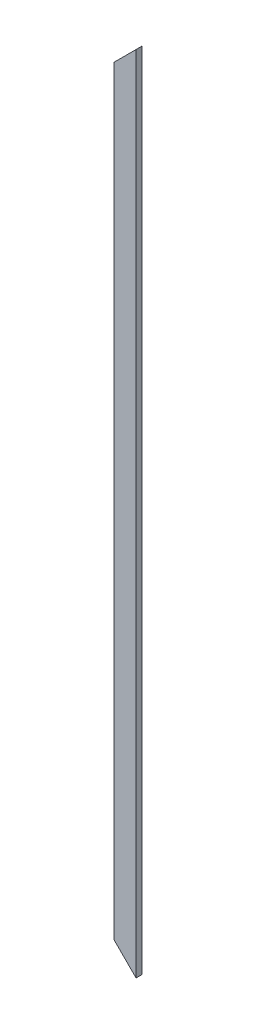
SolidWorks part; units mm, degrees
material "Oak"
ref_plane "Front Plane" through (0, 0, 0) normal (0, 0, 1) x (1, 0, 0)
ref_plane "Top Plane" through (0, 0, 0) normal (0, 1, 0) x (1, 0, 0)
ref_plane "Right Plane" through (0, 0, 0) normal (1, 0, 0) x (0, 0, -1)
sketch "Sketch1" plane through (0, 0, 0) normal (0, 1, 0) x (1, 0, 0)
  line L1 (-69.85, -19.05) -> (69.85, -19.05)
  line L2 (-69.85, -19.05) -> (-69.85, 19.05)
  line L3 (-69.85, 19.05) -> (69.85, 19.05)
  line L4 (69.85, -19.05) -> (69.85, 19.05)
  line L5 (-69.85, -19.05) -> (69.85, 19.05) construction
  line L6 (-69.85, 19.05) -> (69.85, -19.05) construction
  point P0 (0, 0)
  dimension "D1" = 38.1
  dimension "D2" = 139.7
extrude "Boss-Extrude1" add sketch "Sketch1" along normal blind 5054.6 contours L1 L4 L3 L2
sketch "Sketch2" plane through (0, 0, -19.05) normal (0, 0, -1) x (-1, 0, 0)
  line L0 (-69.85, 0) -> (69.85, 139.7)
  line L1 (69.85, 5054.6) -> (69.85, 0) construction
  line L2 (-69.85, 5054.6) -> (69.85, 4914.9)
  line L3 (69.85, 4914.9) -> (69.85, 5054.6)
  line L4 (69.85, 5054.6) -> (-69.85, 5054.6)
  line L5 (69.85, 139.7) -> (69.85, 0)
  line L6 (69.85, 0) -> (-69.85, 0)
extrude "Cut-Extrude1" cut sketch "Sketch2" against normal through all both and the other way through all
